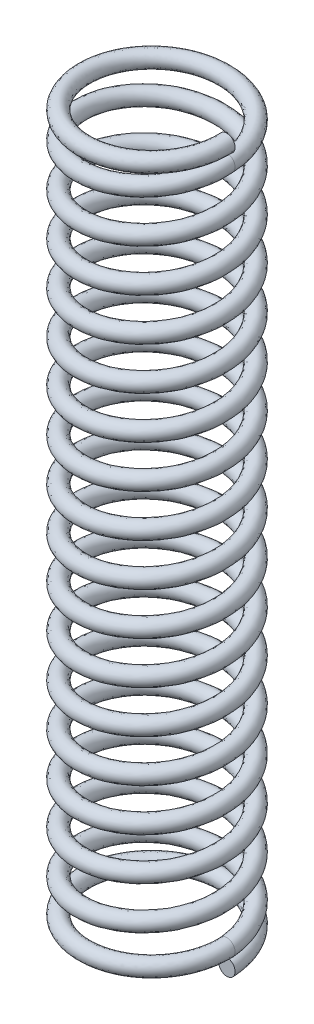
SolidWorks part; units mm, degrees
ref_plane "Front" through (0, 0, 0) normal (0, 0, 1) x (1, 0, 0)
ref_plane "Top" through (0, 0, 0) normal (0, 1, 0) x (1, 0, 0)
ref_plane "Right" through (0, 0, 0) normal (1, 0, 0) x (0, 0, -1)
sketch "Sketch1" plane through (0, 0, 0) normal (0, 0, 1) x (1, 0, 0)
  line L0 (2.486, 25.4) -> (2.486, 25.1079) construction
  line L1 (0, 0) -> (2.486, 0) construction
  line L2 (0, 0) -> (0, 25.4) construction
  line L3 (0, 25.4) -> (2.486, 25.4) construction
  line L4 (2.486, 25.1079) -> (2.486, 25.0825) construction
  line L5 (2.486, 25.0825) -> (2.486, 24.4983) construction
  line L6 (2.486, 24.4983) -> (2.486, 0.9017) construction
  line L7 (2.486, 0.9017) -> (2.486, 0.3175) construction
  line L8 (2.486, 0.3175) -> (2.486, 0.2921) construction
  line L9 (2.486, 0.2921) -> (2.486, 0) construction
  line L10 (2.486, 0) -> (2.7781, 0) construction
  line L11 (2.486, 0.6096) -> (2.7781, 0.6096) construction
  line L12 (2.486, 25.4) -> (2.7781, 25.4) construction
  line L13 (2.486, 25.4) -> (2.486, 25.6921) construction
  line L14 (2.486, 0) -> (2.486, -0.2921) construction
  circle A0 centre (2.486, 25.4) radius 0.2921 construction
  circle A1 centre (2.486, 24.7904) radius 0.2921 construction
  circle A2 centre (2.486, 0.6096) radius 0.2921
  circle A3 centre (2.486, 0) radius 0.2921 construction
  dimension "Wire Dia" = 0.5842
  dimension "D3" = 24.1808
  dimension "D4" = 0.6096
  dimension "D1" = 0.0254
  dimension "Spring-OD" = 5.5562
  dimension "Overall Height" = 25.4
ref_plane "Plane1" through (0, 0.6096, 0) normal (0, 1, 0) x (-1, 0, 0)
sketch "Sketch3" plane through (0, 0.6096, 0) normal (0, 1, 0) x (-1, 0, 0)
  circle A0 centre (0, 0) radius 2.7781
curve "Helix1" pitch 1.5113 height 24.1808 turns 16
sweep "Sweep1" add profiles "Sketch1" path "Helix1"
sketch "Sketch4" plane through (0, 0.6096, 0) normal (0, 1, 0) x (-1, 0, 0)
  circle A0 centre (0, 0) radius 2.7781 construction
  circle A1 centre (0, 0) radius 2.7781
curve "Helix2" pitch 0.6096 height 0.6096 turns 1
sketch "Sketch5" plane through (0, 0, 0) normal (0, 0, 1) x (1, 0, 0)
  circle A0 centre (2.486, 0) radius 0.2921 construction
  circle A1 centre (2.486, 0) radius 0.2921
sweep "Sweep2" add profiles "Sketch5" path "Helix2"
ref_plane "Plane2" through (0, 24.7904, 0) normal (0, 1, 0) x (-1, 0, 0)
sketch "Sketch6" plane through (0, 24.7904, 0) normal (0, 1, 0) x (-1, 0, 0)
  circle A0 centre (0, 0) radius 2.7781 construction
  circle A1 centre (0, 0) radius 2.7781
curve "Helix3" pitch 0.6096 height 0.6096 turns 1
sketch "Sketch7" plane through (0, 0, 0) normal (0, 0, 1) x (1, 0, 0)
  circle A0 centre (2.486, 24.7904) radius 0.2921 construction
  circle A1 centre (2.486, 24.7904) radius 0.2921
sweep "Sweep3" add profiles "Sketch7" path "Helix3"
equation "\"D3@Helix1\"=\"D3@Sketch1\""
equation "\"D3@Helix2\"=\"D4@Sketch1\""
equation "\"D3@Helix3\"=\"D4@Sketch1\""
